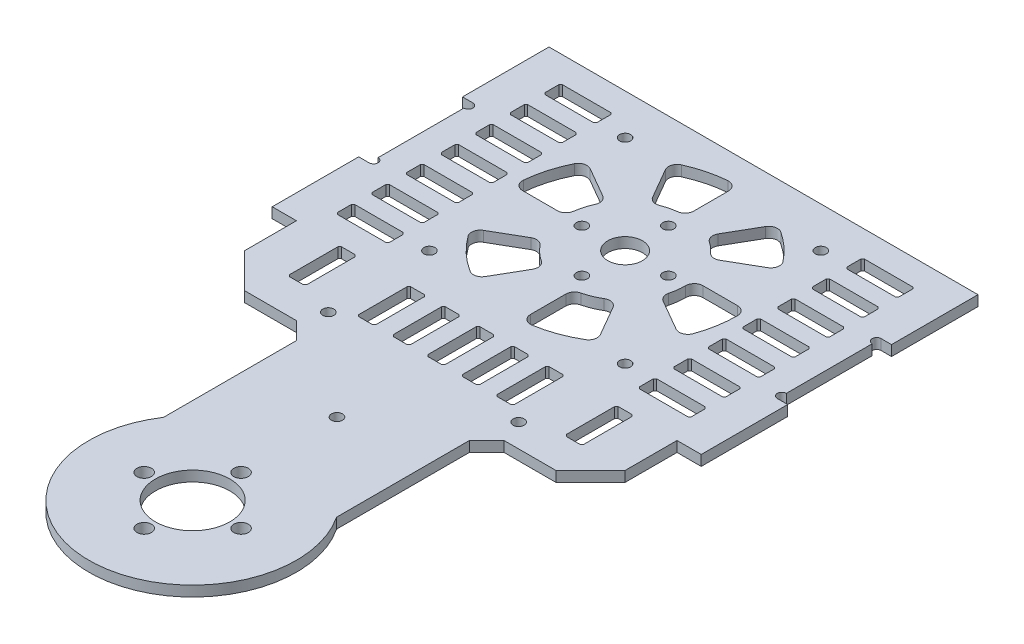
SolidWorks part; units mm, degrees
material "Thornel Mat VMA"
ref_plane "前视基准面" through (0, 0, 0) normal (0, 0, 1) x (1, 0, 0)
ref_plane "上视基准面" through (0, 0, 0) normal (0, 1, 0) x (1, 0, 0)
ref_plane "右视基准面" through (0, 0, 0) normal (1, 0, 0) x (0, 0, -1)
sketch "草图1" plane through (0, 0, 0) normal (0, 1, 0) x (1, 0, 0)
  line L0 (-52.5, 0) -> (52.5, 0) construction
  line L1 (-52.5, 0) -> (-114.5, 0) construction
  line L2 (-114.5, 40) -> (-114.5, -40)
  line L3 (-114.5, 40) -> (75.5, 40)
  line L4 (-114.5, -40) -> (75.5, -40)
  line L5 (75.5, -40) -> (75.5, 40)
  circle A0 centre (52.5, 0) radius 14 construction
  circle A1 centre (38.5, 0) radius 2.1
  circle A2 centre (52.5, 14) radius 2.1
  circle A3 centre (66.5, 0) radius 2.1
  circle A4 centre (52.5, -14) radius 2.1
  circle A5 centre (-40, 0) radius 1.6
  circle A6 centre (-52.5, -12.5) radius 1.6
  circle A7 centre (-65, 0) radius 1.6
  circle A9 centre (52.5, 0) radius 10.75
  circle A10 centre (-52.5, 0) radius 5
  circle A11 centre (-52.5, 0) radius 12.5 construction
  circle A12 centre (-52.5, 12.5) radius 1.6
  point P17 (52.5, 0)
  point P22 (50, 0)
  point P31 (-52.5, 0)
  point P35 (-51.25, 1.25)
  dimension "D2" = 28
  dimension "D3" = 4.2
  dimension "D5" = 21.5
  dimension "D6" = 10
  dimension "D7" = 25
  dimension "D8" = 3.2
  dimension "D1" = 105
  dimension "D10" = 62
  dimension "D11" = 80
  dimension "D12" = 190
  dimension "D4" = 4
  dimension "D9" = 4
extrude "凸台-拉伸1" add sketch "草图1" along normal blind 3
sketch "草图2" plane through (0, 3, 0) normal (0, 1, 0) x (1, 0, 0)
  line L0 (-52.5, 0) -> (-76.6253, 0) construction
  line L1 (-52.5, 0) -> (-52.5, 21.2161) construction
  line L2 (-52.5, 0) -> (-80.7843, 28.2843) construction
  circle A0 centre (-80.7843, 28.2843) radius 1.6
  circle A1 centre (-80.7843, -28.2843) radius 1.6
  circle A2 centre (-24.2157, -28.2843) radius 1.6
  circle A3 centre (-24.2157, 28.2843) radius 1.6
  dimension "D3" = 3.2
  dimension "D1" = 45
  dimension "D2" = 40
extrude "切除-拉伸1" cut sketch "草图2" against normal up to next
sketch "草图3" plane through (0, 3, 0) normal (0, 1, 0) x (1, 0, 0)
  line L0 (-114.5, 40) -> (-114.5, -40) construction
  line L1 (-117.5, -15) -> (-111.5, -15)
  line L2 (-117.5, -15) -> (-117.5, 15)
  line L3 (-117.5, 15) -> (-111.5, 15)
  line L4 (-111.5, -15) -> (-111.5, 15)
  line L5 (-117.5, -15) -> (-111.5, 15) construction
  line L6 (-117.5, 15) -> (-111.5, -15) construction
  point P0 (-114.5, 0)
  dimension "D1" = 6
  dimension "D2" = 30
extrude "切除-拉伸2" cut sketch "草图3" against normal up to next
sketch "草图4" plane through (0, 3, 0) normal (0, 1, 0) x (1, 0, 0)
  line L0 (-111.5, -15) -> (-111.5, 15) construction
  circle A0 centre (-111.5, 13.7) radius 1.3
  circle A1 centre (-111.5, -13.7) radius 1.3
  dimension "D1" = 2.6
  dimension "D2" = 2.6
extrude "切除-拉伸3" cut sketch "草图4" against normal up to next
sketch "草图5" plane through (0, 3, 0) normal (0, 1, 0) x (1, 0, 0)
  line L0 (-111.5, 0) -> (8, 0) construction
  line L1 (-111.5, -12.4) -> (-111.5, 12.4) construction
  line L3 (9.5, 15) -> (6.5, 15)
  line L4 (9.5, 15) -> (9.5, -15)
  line L5 (9.5, -15) -> (6.5, -15)
  line L6 (6.5, 15) -> (6.5, -15)
  line L7 (9.5, 15) -> (6.5, -15) construction
  line L8 (9.5, -15) -> (6.5, 15) construction
  dimension "D1" = 119.5
  dimension "D2" = 30
  dimension "D3" = 3
extrude "切除-拉伸4" cut sketch "草图5" against normal up to next
sketch "草图7" plane through (0, 3, 0) normal (0, 1, 0) x (1, 0, 0)
  line L0 (9.5, -15) -> (9.5, 15) construction
  line L1 (6.5, 15) -> (6.5, -15) construction
  line L2 (9.5, 0) -> (6.5, 0) construction
  circle A0 centre (9.5, 13.7) radius 1.3
  circle A1 centre (6.5, 13.7) radius 1.3
  circle A2 centre (6.5, -13.7) radius 1.3
  circle A3 centre (9.5, -13.7) radius 1.3
  dimension "D1" = 2.6
  dimension "D2" = 2.6
extrude "切除-拉伸6" cut sketch "草图7" against normal up to next
sketch "草图8" plane through (0, 3, 0) normal (0, 1, 0) x (1, 0, 0)
  line L0 (-80.7843, 28.2843) -> (-80.7843, -28.2843) construction
  line L1 (-80.7843, 0) -> (-111.5, 0) construction
  line L2 (-111.5, -12.4) -> (-111.5, 12.4) construction
  line L3 (-103.6421, 2) -> (-103.1421, 2.5)
  line L4 (-103.1421, 2.5) -> (-89.1421, 2.5)
  line L5 (-103.6421, 2) -> (-103.6421, -2)
  line L6 (-103.1421, -2.5) -> (-89.1421, -2.5)
  line L7 (-88.6421, 2) -> (-88.6421, -2)
  line L8 (-103.6421, 2.5) -> (-88.6421, -2.5) construction
  line L9 (-103.6421, -2.5) -> (-88.6421, 2.5) construction
  line L10 (-103.6421, -2) -> (-103.1421, -2.5)
  line L11 (-89.1421, 2.5) -> (-88.6421, 2)
  line L12 (-88.6421, -2) -> (-89.1421, -2.5)
  line L13 (-103.6421, 12) -> (-103.6421, 8)
  line L14 (-103.6421, 12) -> (-103.1421, 12.5)
  line L15 (-103.1421, 12.5) -> (-89.1421, 12.5)
  line L16 (-89.1421, 12.5) -> (-88.6421, 12)
  line L17 (-88.6421, 12) -> (-88.6421, 8)
  line L18 (-88.6421, 8) -> (-89.1421, 7.5)
  line L19 (-103.1421, 7.5) -> (-89.1421, 7.5)
  line L20 (-103.6421, 8) -> (-103.1421, 7.5)
  line L21 (-103.6421, 22) -> (-103.6421, 18)
  line L22 (-103.6421, 22) -> (-103.1421, 22.5)
  line L23 (-103.1421, 22.5) -> (-89.1421, 22.5)
  line L24 (-89.1421, 22.5) -> (-88.6421, 22)
  line L25 (-88.6421, 22) -> (-88.6421, 18)
  line L26 (-88.6421, 18) -> (-89.1421, 17.5)
  line L27 (-103.1421, 17.5) -> (-89.1421, 17.5)
  line L28 (-103.6421, 18) -> (-103.1421, 17.5)
  line L29 (-103.6421, 32) -> (-103.6421, 28)
  line L30 (-103.6421, 32) -> (-103.1421, 32.5)
  line L31 (-103.1421, 32.5) -> (-89.1421, 32.5)
  line L32 (-89.1421, 32.5) -> (-88.6421, 32)
  line L33 (-88.6421, 32) -> (-88.6421, 28)
  line L34 (-88.6421, 28) -> (-89.1421, 27.5)
  line L35 (-103.1421, 27.5) -> (-89.1421, 27.5)
  line L36 (-103.6421, 28) -> (-103.1421, 27.5)
  line L37 (-103.6421, -28) -> (-103.1421, -27.5)
  line L38 (-103.1421, -27.5) -> (-89.1421, -27.5)
  line L39 (-88.6421, -28) -> (-89.1421, -27.5)
  line L40 (-88.6421, -32) -> (-88.6421, -28)
  line L41 (-89.1421, -32.5) -> (-88.6421, -32)
  line L42 (-103.6421, -32) -> (-103.1421, -32.5)
  line L43 (-103.6421, -32) -> (-103.6421, -28)
  line L44 (-103.6421, -18) -> (-103.1421, -17.5)
  line L45 (-103.1421, -17.5) -> (-89.1421, -17.5)
  line L46 (-88.6421, -18) -> (-89.1421, -17.5)
  line L47 (-88.6421, -22) -> (-88.6421, -18)
  line L48 (-89.1421, -22.5) -> (-88.6421, -22)
  line L49 (-103.1421, -22.5) -> (-89.1421, -22.5)
  line L50 (-103.6421, -22) -> (-103.1421, -22.5)
  line L51 (-103.6421, -22) -> (-103.6421, -18)
  line L52 (-103.6421, -8) -> (-103.1421, -7.5)
  line L53 (-103.1421, -7.5) -> (-89.1421, -7.5)
  line L54 (-88.6421, -8) -> (-89.1421, -7.5)
  line L55 (-88.6421, -12) -> (-88.6421, -8)
  line L56 (-89.1421, -12.5) -> (-88.6421, -12)
  line L57 (-103.1421, -12.5) -> (-89.1421, -12.5)
  line L58 (-103.6421, -12) -> (-103.1421, -12.5)
  line L59 (-103.6421, -12) -> (-103.6421, -8)
  line L60 (-103.1421, -32.5) -> (-89.1421, -32.5)
  line L61 (-52.5, 0) -> (-52.5, -34.4819) construction
  line L62 (-1.3579, -2.5) -> (-16.3579, 2.5) construction
  line L63 (-1.3579, 2.5) -> (-16.3579, -2.5) construction
  line L64 (-24.2157, 0) -> (6.5, 0) construction
  line L65 (-1.8579, -32.5) -> (-15.8579, -32.5)
  line L66 (-1.3579, -12) -> (-1.3579, -8)
  line L67 (-1.3579, -12) -> (-1.8579, -12.5)
  line L68 (-1.8579, -12.5) -> (-15.8579, -12.5)
  line L69 (-15.8579, -12.5) -> (-16.3579, -12)
  line L70 (-16.3579, -12) -> (-16.3579, -8)
  line L71 (-16.3579, -8) -> (-15.8579, -7.5)
  line L72 (-1.8579, -7.5) -> (-15.8579, -7.5)
  line L73 (-1.3579, -8) -> (-1.8579, -7.5)
  line L74 (-1.3579, -22) -> (-1.3579, -18)
  line L75 (-1.3579, -22) -> (-1.8579, -22.5)
  line L76 (-1.8579, -22.5) -> (-15.8579, -22.5)
  line L77 (-15.8579, -22.5) -> (-16.3579, -22)
  line L78 (-16.3579, -22) -> (-16.3579, -18)
  line L79 (-16.3579, -18) -> (-15.8579, -17.5)
  line L80 (-1.8579, -17.5) -> (-15.8579, -17.5)
  line L81 (-1.3579, -18) -> (-1.8579, -17.5)
  line L82 (-1.3579, -32) -> (-1.3579, -28)
  line L83 (-1.3579, -32) -> (-1.8579, -32.5)
  line L84 (-15.8579, -32.5) -> (-16.3579, -32)
  line L85 (-16.3579, -32) -> (-16.3579, -28)
  line L86 (-16.3579, -28) -> (-15.8579, -27.5)
  line L87 (-1.8579, -27.5) -> (-15.8579, -27.5)
  line L88 (-1.3579, -28) -> (-1.8579, -27.5)
  line L89 (-1.3579, 28) -> (-1.8579, 27.5)
  line L90 (-1.8579, 27.5) -> (-15.8579, 27.5)
  line L91 (-16.3579, 28) -> (-15.8579, 27.5)
  line L92 (-16.3579, 32) -> (-16.3579, 28)
  line L93 (-15.8579, 32.5) -> (-16.3579, 32)
  line L94 (-1.8579, 32.5) -> (-15.8579, 32.5)
  line L95 (-1.3579, 32) -> (-1.8579, 32.5)
  line L96 (-1.3579, 32) -> (-1.3579, 28)
  line L97 (-1.3579, 18) -> (-1.8579, 17.5)
  line L98 (-1.8579, 17.5) -> (-15.8579, 17.5)
  line L99 (-16.3579, 18) -> (-15.8579, 17.5)
  line L100 (-16.3579, 22) -> (-16.3579, 18)
  line L101 (-15.8579, 22.5) -> (-16.3579, 22)
  line L102 (-1.8579, 22.5) -> (-15.8579, 22.5)
  line L103 (-1.3579, 22) -> (-1.8579, 22.5)
  line L104 (-1.3579, 22) -> (-1.3579, 18)
  line L105 (-1.3579, 8) -> (-1.8579, 7.5)
  line L106 (-1.8579, 7.5) -> (-15.8579, 7.5)
  line L107 (-16.3579, 8) -> (-15.8579, 7.5)
  line L108 (-16.3579, 12) -> (-16.3579, 8)
  line L109 (-15.8579, 12.5) -> (-16.3579, 12)
  line L110 (-1.8579, 12.5) -> (-15.8579, 12.5)
  line L111 (-1.3579, 12) -> (-1.8579, 12.5)
  line L112 (-1.3579, 12) -> (-1.3579, 8)
  line L113 (-16.3579, -2) -> (-15.8579, -2.5)
  line L114 (-15.8579, 2.5) -> (-16.3579, 2)
  line L115 (-1.3579, -2) -> (-1.8579, -2.5)
  line L116 (-16.3579, 2) -> (-16.3579, -2)
  line L117 (-1.8579, -2.5) -> (-15.8579, -2.5)
  line L118 (-1.3579, 2) -> (-1.3579, -2)
  line L119 (-1.8579, 2.5) -> (-15.8579, 2.5)
  line L120 (-1.3579, 2) -> (-1.8579, 2.5)
  point P8 (-96.1421, 0)
  point P134 (-8.8579, 0)
  dimension "D1" = 15
  dimension "D2" = 5
  dimension "D3" = 4
extrude "切除-拉伸7" cut sketch "草图8" against normal up to next
sketch "草图9" plane through (0, 3, 0) normal (0, 1, 0) x (1, 0, 0)
  line L0 (-52.5, 19.8431) -> (-52.5, 29.8957)
  line L1 (-43.2569, 17.6772) -> (-38.2453, 26.3576)
  line L2 (-36.4494, 11.2864) -> (-27.6556, 16.3634)
  line L3 (-32.5, 2.5) -> (-22.5, 2.5)
  line L4 (-34.3764, -7.1314) -> (-25.4984, -12.2571)
  line L5 (-40.0737, -15.917) -> (-35.0733, -24.578)
  line L6 (-50.2263, -19.4219) -> (-50.2263, -29.6178)
  line L7 (-61.2391, -18.016) -> (-66.2437, -26.6844)
  line L8 (-69.3589, -10.3394) -> (-78.086, -15.378)
  line L9 (-72.3133, 0.2263) -> (-82.3759, 0.2263)
  line L10 (-69.4371, 10.4855) -> (-78.1232, 15.5004)
  line L11 (-61.9263, 17.3853) -> (-66.965, 26.1126)
  arc A0 (-66.1578, -10.9414) -> (-62.0411, -14.6703) centre (-52.5, 0) ccw
  arc A1 (-78.864, -19.005) -> (-69.7345, -27.554) centre (-52.5, 0) ccw
  arc A2 (-68.4137, 7.2803) -> (-69.8366, 2.3855) centre (-52.5, 0) ccw
  arc A3 (-81.6126, 14.4466) -> (-84.8655, 2.9535) centre (-52.5, 0) ccw
  arc A4 (-54.6875, 17.3627) -> (-58.8535, 16.3059) centre (-52.5, 0) ccw
  arc A5 (-55.2083, 32.387) -> (-65.8249, 29.6428) centre (-52.5, 0) ccw
  arc A6 (-39.5494, 11.77) -> (-42.5179, 14.3738) centre (-52.5, 0) ccw
  arc A7 (-26.9394, 20.0725) -> (-34.7119, 27.1999) centre (-52.5, 0) ccw
  arc A8 (-35.5481, -4.3456) -> (-35, 0) centre (-52.5, 0) ccw
  arc A9 (-21.8942, -10.9331) -> (-20, 0) centre (-52.5, 0) ccw
  arc A10 (-47.3285, -32.0859) -> (-35.9666, -27.9803) centre (-52.5, 0) ccw
  arc A11 (-48.323, -16.9942) -> (-43.5214, -15.0212) centre (-52.5, 0) ccw
  arc A12 (-21.8942, -10.9331) -> (-25.4984, -12.2571) centre (-24.2484, -10.0921) cw
  arc A13 (-34.3764, -7.1314) -> (-35.5481, -4.3456) centre (-33.1264, -4.9664) cw
  arc A14 (-32.5, 2.5) -> (-35, 0) centre (-32.5, 0) ccw
  arc A15 (-38.2453, 26.3576) -> (-34.7119, 27.1999) centre (-36.0803, 25.1076) cw
  arc A16 (-26.9394, 20.0725) -> (-27.6556, 16.3634) centre (-28.9056, 18.5285) cw
  arc A17 (-36.4494, 11.2864) -> (-39.5494, 11.77) centre (-37.6994, 13.4514) cw
  arc A18 (-42.5179, 14.3738) -> (-43.2569, 17.6772) centre (-41.0919, 16.4272) cw
  arc A19 (-52.5, 19.8431) -> (-54.6875, 17.3627) centre (-55, 19.8431) cw
  arc A20 (-58.8535, 16.3059) -> (-61.9263, 17.3853) centre (-59.7612, 18.6353) cw
  arc A21 (-52.5, 29.8957) -> (-55.2083, 32.387) centre (-55, 29.8957) ccw
  arc A22 (-65.8249, 29.6428) -> (-66.965, 26.1126) centre (-64.7999, 27.3626) ccw
  arc A23 (-69.8366, 2.3855) -> (-72.3133, 0.2263) centre (-72.3133, 2.7263) cw
  arc A24 (-68.4137, 7.2803) -> (-69.4371, 10.4855) centre (-70.6871, 8.3204) ccw
  arc A25 (-78.1232, 15.5004) -> (-81.6126, 14.4466) centre (-79.3732, 13.3353) ccw
  arc A26 (-82.3759, 0.2263) -> (-84.8655, 2.9535) centre (-82.3759, 2.7263) cw
  arc A27 (-61.2391, -18.016) -> (-62.0411, -14.6703) centre (-63.4041, -16.766) ccw
  arc A28 (-66.1578, -10.9414) -> (-69.3589, -10.3394) centre (-68.1089, -12.5045) ccw
  arc A29 (-66.2437, -26.6844) -> (-69.7345, -27.554) centre (-68.4088, -25.4344) cw
  arc A30 (-78.864, -19.005) -> (-78.086, -15.378) centre (-76.836, -17.543) cw
  arc A31 (-35.0733, -24.578) -> (-35.9666, -27.9803) centre (-37.2384, -25.828) cw
  arc A32 (-47.3285, -32.0859) -> (-50.2263, -29.6178) centre (-47.7263, -29.6178) cw
  arc A33 (-40.0737, -15.917) -> (-43.5214, -15.0212) centre (-42.2388, -17.167) ccw
  arc A34 (-50.2263, -19.4219) -> (-48.323, -16.9942) centre (-47.7263, -19.4219) cw
  arc A35 (-20, 0) -> (-22.5, 2.5) centre (-22.5, 0) ccw
  point P31 (-51.3632, 1.3632)
  point P43 (-52.5, 17.5)
  point P48 (-52.5, 32.5)
  dimension "D1" = 35
  dimension "D2" = 65
  dimension "D4" = 2.5
  dimension "D5" = 2.5
  dimension "D3" = 12
extrude "切除-拉伸8" cut sketch "草图9" against normal up to next
sketch "草图10" plane through (0, 3, 0) normal (0, 1, 0) x (1, 0, 0)
  line L0 (29.5, 40) -> (75.5, 8.5372)
  line L1 (75.5, 40) -> (-114.5, 40) construction
  line L2 (75.5, -40) -> (75.5, 40) construction
  line L3 (75.5, 8.5372) -> (75.5, -12.7896)
  line L4 (75.5, -12.7896) -> (29.5, -40)
  line L5 (-114.5, -40) -> (75.5, -40) construction
  arc A0 (29.5, -40) -> (29.5, 40) centre (52.5, 0) ccw
extrude "凸台-拉伸2" add sketch "草图10" against normal up to surface (83.9662 mm away)
sketch "草图14" plane through (0, 0, 0) normal (0, -1, 0) x (1, 0, 0)
  line L0 (9.5, 0) -> (9.5, -55.7871)
  line L1 (9.5, -12.4) -> (9.5, 12.4) construction
  line L2 (9.5, -55.7871) -> (108.7563, -55.7871)
  line L3 (108.7563, -55.7871) -> (108.7563, 62.2798)
  line L4 (108.7563, 62.2798) -> (9.5, 62.2798)
  line L5 (9.5, 62.2798) -> (9.5, 0)
extrude "切除-拉伸9" cut sketch "草图14" against normal up to next
sketch "草图15" plane through (0, 0, 0) normal (0, -1, 0) x (1, 0, 0)
  line L0 (-52.5, 0) -> (-52.5, 125) construction
  line L1 (-77.5, 40) -> (-77.5, 108.4169)
  line L2 (-114.5, 40) -> (9.5, 40) construction
  line L3 (-27.5, 40) -> (-27.5, 108.4169)
  line L4 (-27.5, 40) -> (-77.5, 40)
  circle A0 centre (-52.5, 125) radius 10.75
  circle A1 centre (-52.5, 125) radius 14 construction
  circle A2 centre (-66.5, 125) radius 2.1
  circle A3 centre (-52.5, 139) radius 2.1
  circle A4 centre (-38.5, 125) radius 2.1
  circle A5 centre (-52.5, 111) radius 2.1
  arc A6 (-27.5, 108.4169) -> (-77.5, 108.4169) centre (-52.5, 125) ccw
  point P16 (-52.5, 150)
  point P23 (-52.5, 120)
  point P24 (-52.5, 125)
  dimension "D2" = 21.5
  dimension "D3" = 28
  dimension "D4" = 4.2
  dimension "D6" = 60
  dimension "D1" = 125
  dimension "D7" = 25
  dimension "D5" = 4
extrude "凸台-拉伸3" add sketch "草图15" against normal up to surface (83.9662 mm away)
sketch "草图16" plane through (0, 0, 0) normal (0, -1, 0) x (1, 0, 0)
  line L0 (-27.5, 40) -> (2.5, 40)
  line L1 (-27.5, 40) -> (9.5, 40) construction
  line L2 (2.5, 40) -> (-27.5, 65)
  line L3 (-27.5, 40) -> (-27.5, 108.4169) construction
  line L4 (-27.5, 65) -> (-27.5, 40)
  line L5 (2.5, 40) -> (-27.5, 40)
  line L6 (-52.5, 125) -> (-52.5, 0) construction
  line L7 (-77.5, 40) -> (-107.5, 40)
  line L8 (-107.5, 40) -> (-77.5, 65)
  line L9 (-77.5, 65) -> (-77.5, 40)
  dimension "D1" = 30
  dimension "D2" = 25
extrude "凸台-拉伸4" add sketch "草图16" against normal up to surface (3 mm away) contours L2 L4 L0 | L9 L8 L7 up to face at (-54.35, 3, 17.1708)
sketch "草图18" plane through (0, 0, 0) normal (0, -1, 0) x (1, 0, 0)
  line L0 (-27.5, 65) -> (2.5, 65)
  line L1 (2.5, 65) -> (2.5, 40)
  line L2 (2.5, 40) -> (-27.5, 65)
  line L3 (-52.5, 125) -> (-52.5, 65) construction
  line L4 (-77.5, 65) -> (-107.5, 65)
  line L5 (-107.5, 40) -> (-77.5, 65)
  line L6 (-107.5, 65) -> (-107.5, 40)
extrude "凸台-拉伸5" add sketch "草图18" against normal up to surface (3 mm away) up to face at (-52.8182, 3, 21.5189)
sketch "草图17" plane through (0, 0, 0) normal (0, -1, 0) x (1, 0, 0)
  line L0 (-24.2157, 28.2843) -> (-80.7843, 28.2843) construction
  line L1 (-52.5, 28.2843) -> (-52.5, 58.2843) construction
  line L2 (-25, 58.2843) -> (-80, 58.2843) construction
  circle A0 centre (-25, 58.2843) radius 1.6
  circle A1 centre (-80, 58.2843) radius 1.6
  dimension "D3" = 3.2
  dimension "D4" = 3.2
  dimension "D1" = 55
  dimension "D2" = 30
extrude "切除-拉伸10" cut sketch "草图17" against normal up to next
sketch "草图19" plane through (0, 0, 0) normal (0, -1, 0) x (1, 0, 0)
  line L0 (-24.2157, 28.2843) -> (-80.7843, 28.2843) construction
  line L1 (-52.5, 28.2843) -> (-52.5, 83.2843) construction
  circle A0 centre (-52.5, 83.2843) radius 1.6
  dimension "D2" = 3.2
  dimension "D1" = 55
extrude "切除-拉伸11" cut sketch "草图19" against normal up to next
chamfer "倒角1" distance 10 angle 45 2 edges at (-107.5, 1.5, 65) (2.5, 1.5, 65)
chamfer "倒角2" distance 5 angle 45 2 edges at (-77.5, 1.5, 65) (-27.5, 1.5, 65)
sketch "草图20" plane through (0, 0, 0) normal (0, -1, 0) x (1, 0, 0)
  line L0 (2.5, 47.5) -> (-107.5, 47.5) construction
  line L1 (2.5, 40) -> (2.5, 55) construction
  line L2 (-107.5, 55) -> (-107.5, 40) construction
  line L3 (-50, 54.5) -> (-50.5, 55)
  line L4 (-50.5, 40) -> (-54.5, 40)
  line L5 (-50, 40.5) -> (-50, 54.5)
  line L6 (-50.5, 55) -> (-54.5, 55)
  line L7 (-55, 40.5) -> (-55, 54.5)
  line L8 (-50, 40) -> (-55, 55) construction
  line L9 (-50, 55) -> (-55, 40) construction
  line L10 (-54.5, 55) -> (-55, 54.5)
  line L11 (-50.5, 40) -> (-50, 40.5)
  line L12 (-54.5, 40) -> (-55, 40.5)
  line L13 (-40, 40.5) -> (-40, 54.5)
  line L14 (-40, 54.5) -> (-40.5, 55)
  line L15 (-40.5, 55) -> (-44.5, 55)
  line L16 (-44.5, 55) -> (-45, 54.5)
  line L17 (-45, 40.5) -> (-45, 54.5)
  line L18 (-44.5, 40) -> (-45, 40.5)
  line L19 (-40.5, 40) -> (-44.5, 40)
  line L20 (-40.5, 40) -> (-40, 40.5)
  line L21 (-30, 40.5) -> (-30, 54.5)
  line L22 (-30, 54.5) -> (-30.5, 55)
  line L23 (-30.5, 55) -> (-34.5, 55)
  line L24 (-34.5, 55) -> (-35, 54.5)
  line L25 (-35, 40.5) -> (-35, 54.5)
  line L26 (-34.5, 40) -> (-35, 40.5)
  line L27 (-30.5, 40) -> (-34.5, 40)
  line L28 (-30.5, 40) -> (-30, 40.5)
  line L29 (-10, 40.5) -> (-10, 54.5)
  line L30 (-15, 40.5) -> (-15, 54.5)
  line L31 (-10.5, 55) -> (-14.5, 55)
  line L32 (-10.5, 40) -> (-14.5, 40)
  line L33 (-10.5, 40) -> (-10, 40.5)
  line L34 (-14.5, 40) -> (-15, 40.5)
  line L35 (-10, 54.5) -> (-10.5, 55)
  line L36 (-14.5, 55) -> (-15, 54.5)
  line L37 (-52.5, 47.5) -> (-52.5, 72.0791) construction
  line L38 (-64.5, 40) -> (-65, 40.5)
  line L39 (-64.5, 40) -> (-60.5, 40)
  line L40 (-60.5, 40) -> (-60, 40.5)
  line L41 (-60, 40.5) -> (-60, 54.5)
  line L42 (-60.5, 55) -> (-60, 54.5)
  line L43 (-64.5, 55) -> (-60.5, 55)
  line L44 (-65, 54.5) -> (-64.5, 55)
  line L45 (-65, 40.5) -> (-65, 54.5)
  line L46 (-75, 54.5) -> (-74.5, 55)
  line L47 (-74.5, 55) -> (-70.5, 55)
  line L48 (-70.5, 55) -> (-70, 54.5)
  line L49 (-70, 40.5) -> (-70, 54.5)
  line L50 (-70.5, 40) -> (-70, 40.5)
  line L51 (-74.5, 40) -> (-70.5, 40)
  line L52 (-75, 40.5) -> (-75, 54.5)
  line L53 (-74.5, 40) -> (-75, 40.5)
  line L54 (-95, 54.5) -> (-94.5, 55)
  line L55 (-94.5, 55) -> (-90.5, 55)
  line L56 (-90.5, 55) -> (-90, 54.5)
  line L57 (-90, 40.5) -> (-90, 54.5)
  line L58 (-90.5, 40) -> (-90, 40.5)
  line L59 (-94.5, 40) -> (-90.5, 40)
  line L60 (-94.5, 40) -> (-95, 40.5)
  line L61 (-95, 40.5) -> (-95, 54.5)
  point P6 (-52.5, 47.5)
  dimension "D1" = 15
  dimension "D2" = 5
  dimension "D3" = 3
  dimension "D4" = 2
extrude "切除-拉伸12" cut sketch "草图20" against normal up to next
